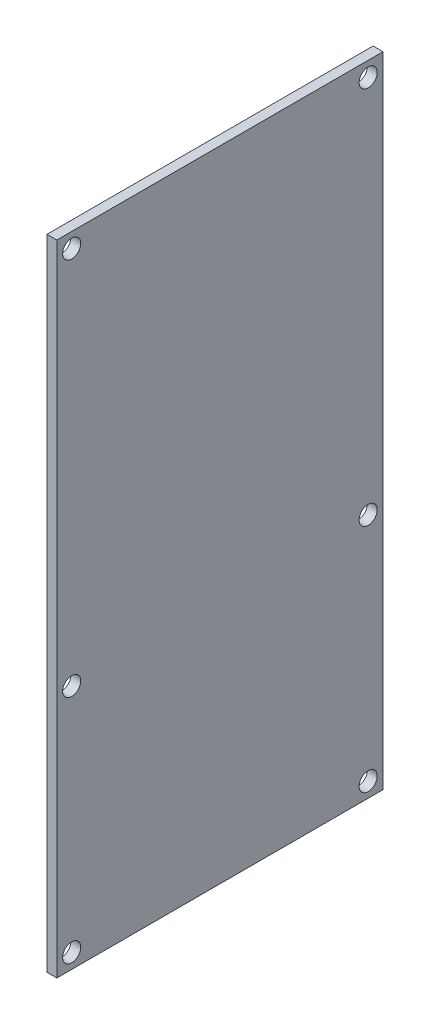
SolidWorks part; units mm, degrees
ref_plane "Front Plane" through (0, 0, 0) normal (0, 0, 1) x (1, 0, 0)
ref_plane "Top Plane" through (0, 0, 0) normal (0, 1, 0) x (1, 0, 0)
ref_plane "Right Plane" through (0, 0, 0) normal (1, 0, 0) x (0, 0, -1)
sketch "Sketch1" plane through (45.0117, 0, 0) normal (1, 0, 0) x (0, 0, -1)
  line L0 (-33.2693, 104.5) -> (-33.2693, -89.5)
  line L1 (-33.7693, 105) -> (66.2307, 105) construction
  line L2 (-33.7693, 105) -> (-33.7693, -90) construction
  line L3 (-33.7693, -90) -> (66.2307, -90) construction
  line L4 (66.2307, 105) -> (66.2307, -90) construction
  line L5 (-33.2693, -89.5) -> (65.7307, -89.5)
  line L6 (65.7307, 104.5) -> (65.7307, -89.5)
  line L7 (-33.2693, 104.5) -> (65.7307, 104.5)
  dimension "D1" = 0.5
extrude "Boss-Extrude1" add sketch "Sketch1" along normal blind 3
sketch "Sketch2" plane through (48.0117, 0, 0) normal (1, 0, 0) x (0, 0, -1)
  line L0 (-33.2693, 104.5) -> (-33.2693, -89.5) construction
  line L1 (65.7307, 104.5) -> (-33.2693, 104.5) construction
  line L2 (-33.2693, -89.5) -> (65.7307, -89.5) construction
  line L3 (65.7307, -89.5) -> (65.7307, 104.5) construction
  circle A0 centre (-28.7693, 100) radius 2.75
  circle A1 centre (61.2307, 100) radius 2.75
  circle A2 centre (-28.7693, -85) radius 2.75
  circle A3 centre (61.2307, -85) radius 2.75
  circle A4 centre (-28.7693, -15) radius 2.75
  circle A5 centre (61.2307, -15) radius 2.75
  dimension "D1" = 5.5
  dimension "D2" = 4.5
  dimension "D3" = 4.5
  dimension "D4" = 4.5
  dimension "D5" = 4.5
  dimension "D6" = 70
extrude "Cut-Extrude1" cut sketch "Sketch2" against normal through all
